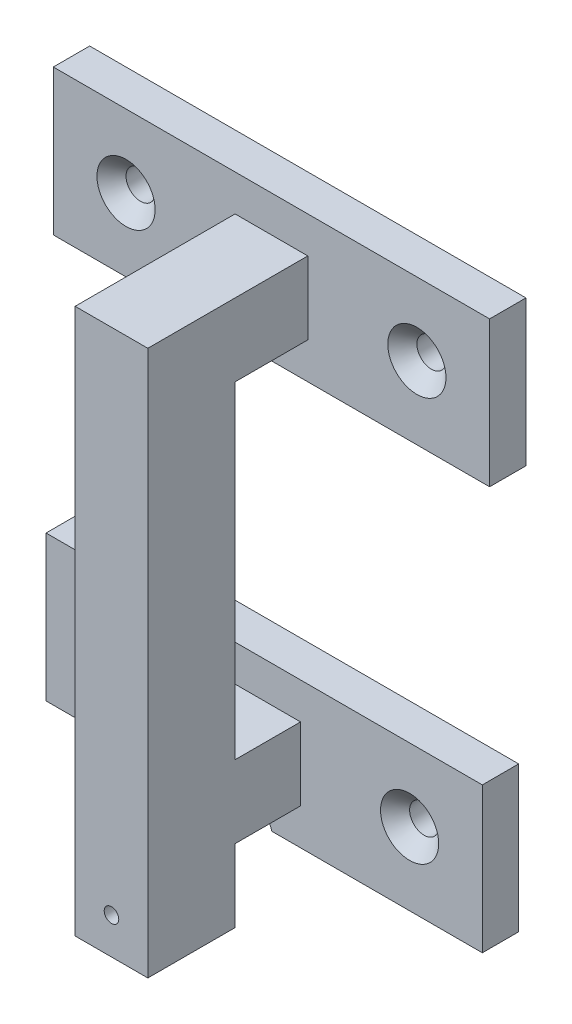
SolidWorks part; units mm, degrees
material "ABS"
ref_plane "Front Plane" through (0, 0, 0) normal (0, 0, 1) x (1, 0, 0)
ref_plane "Top Plane" through (0, 0, 0) normal (0, 1, 0) x (1, 0, 0)
ref_plane "Right Plane" through (0, 0, 0) normal (1, 0, 0) x (0, 0, -1)
sketch "Sketch1" plane through (0, 0, 0) normal (0, 0, 1) x (1, 0, 0)
  line L1 (-5, -5) -> (5, -5)
  line L2 (-5, -5) -> (-5, 5)
  line L3 (-5, 5) -> (5, 5)
  line L4 (5, -5) -> (5, 5)
  line L5 (-5, -5) -> (5, 5) construction
  line L6 (-5, 5) -> (5, -5) construction
  point P0 (0, 0)
  point P5 (0, 0)
  dimension "D1" = 10
  dimension "D2" = 10
extrude "Boss-Extrude1" add sketch "Sketch1" along normal blind 5
sketch "Sketch2" plane through (0, 0, 0) normal (0, 0, -1) x (-1, 0, 0)
  line L1 (-5, -5) -> (5, -5)
  line L2 (-5, -5) -> (-5, 5)
  line L3 (-5, 5) -> (5, 5)
  line L4 (5, -5) -> (5, 5)
  line L5 (-5, -5) -> (5, 5) construction
  line L6 (-5, 5) -> (5, -5) construction
  point P0 (0, 0)
extrude "Boss-Extrude2" add sketch "Sketch2" along normal blind 20
sketch "Sketch3" plane through (0, 0, -20) normal (0, 0, -1) x (-1, 0, 0)
  line L0 (0, -10) -> (0, -7.6109) construction
  line L1 (-30, -10) -> (30, -10)
  line L2 (-30, -10) -> (-30, 10)
  line L3 (-30, 10) -> (30, 10)
  line L4 (30, -10) -> (30, 10)
  line L5 (-30, -10) -> (30, 10) construction
  line L6 (-30, 10) -> (30, -10) construction
  circle A0 centre (20, 0) radius 2
  circle A1 centre (-20, 0) radius 2
  point P0 (0, 0)
  dimension "D3" = 4
  dimension "D1" = 60
  dimension "D2" = 20
  dimension "D4" = 10
extrude "Boss-Extrude3" add sketch "Sketch3" against normal blind 5
sketch "Sketch4" plane through (0, -5, 0) normal (0, -1, 0) x (1, 0, 0)
  line L0 (5, 5) -> (5, -15) construction
  line L1 (-5, -6) -> (5, -6)
  line L2 (-5, -6) -> (-5, 6)
  line L3 (-5, 6) -> (5, 6)
  line L4 (5, -6) -> (5, 6)
  line L5 (-5, -6) -> (5, 6) construction
  line L6 (-5, 6) -> (5, -6) construction
  point P0 (0, 0)
  dimension "D1" = 12
extrude "Boss-Extrude4" add sketch "Sketch4" along normal blind 10 and the other way blind 65
sketch "Sketch5" plane through (0, -15, 0) normal (0, -1, 0) x (-1, 0, 0)
  line L1 (2.05, 1.55) -> (-2.05, 1.55)
  line L2 (2.05, 1.55) -> (2.05, -1.55)
  line L3 (2.05, -1.55) -> (-2.05, -1.55)
  line L4 (-2.05, 1.55) -> (-2.05, -1.55)
  line L5 (2.05, 1.55) -> (-2.05, -1.55) construction
  line L6 (2.05, -1.55) -> (-2.05, 1.55) construction
  line L7 (-2.05, 1.05) -> (-3.65, 1.05)
  line L8 (-2.05, 1.05) -> (-2.05, -1.05)
  line L9 (-2.05, -1.05) -> (-3.65, -1.05)
  line L10 (-3.65, 1.05) -> (-3.65, -1.05)
  line L11 (-2.05, 1.05) -> (-3.65, -1.05) construction
  line L12 (-2.05, -1.05) -> (-3.65, 1.05) construction
  point P0 (0, 0)
  point P5 (-2.85, 0)
  dimension "D1" = 4.1
  dimension "D2" = 3.1
  dimension "D3" = 1.6
  dimension "D4" = 2.1
  dimension "D5" = 0.8
  dimension "D6" = 1.55
extrude "Cut-Extrude1" cut sketch "Sketch5" against normal blind 13 contours L1 L4 L3 L2 | L7 L10 L9 L4
sketch "Sketch7" plane through (0, 0, 6) normal (0, 0, 1) x (1, 0, 0)
  line L0 (5, -15) -> (-5, -15) construction
  line L1 (5, -15) -> (5, 60) construction
  circle A0 centre (0, -10) radius 1
  dimension "D1" = 2
  dimension "D2" = 5
  dimension "D3" = 5
extrude "Cut-Extrude3" cut sketch "Sketch7" against normal through all
sketch "Sketch10" plane through (0, 0, -6) normal (0, 0, -1) x (-1, 0, 0)
  line L0 (5, 60) -> (5, 5) construction
  line L1 (-5, 50) -> (5, 50)
  line L2 (-5, 50) -> (-5, 60)
  line L3 (-5, 60) -> (5, 60)
  line L4 (5, 50) -> (5, 60)
  line L5 (-5, 50) -> (5, 60) construction
  line L6 (-5, 60) -> (5, 50) construction
  line L7 (5, 60) -> (-5, 60) construction
  point P0 (0, 55)
  point P9 (0, 60)
  dimension "D1" = 10
  dimension "D2" = 10
  dimension "D3" = 5
extrude "Boss-Extrude6" add sketch "Sketch10" along normal blind 10
sketch "Sketch12" plane through (0, 0, -16) normal (0, 0, -1) x (-1, 0, 0)
  line L0 (5, 60) -> (-5, 60) construction
  line L1 (-30, 45) -> (30, 45)
  line L2 (-30, 45) -> (-30, 65)
  line L3 (-30, 65) -> (30, 65)
  line L4 (30, 45) -> (30, 65)
  line L5 (-30, 45) -> (30, 65) construction
  line L6 (-30, 65) -> (30, 45) construction
  line L7 (0, 65) -> (0, 45) construction
  line L9 (5, 50) -> (5, 60) construction
  circle A0 centre (20, 55) radius 2
  circle A1 centre (-20, 55) radius 2
  point P0 (0, 55)
  dimension "D5" = 4
  dimension "D6" = 10
  dimension "D1" = 60
  dimension "D2" = 20
  dimension "D3" = 5
  dimension "D4" = 5
extrude "Boss-Extrude7" add sketch "Sketch12" along normal blind 5
chamfer "Chamfer1" distance 2 angle 45 4 edges at (-22, 0, -15) (-18, 55, -16) (18, 55, -16) (22, 0, -15)
